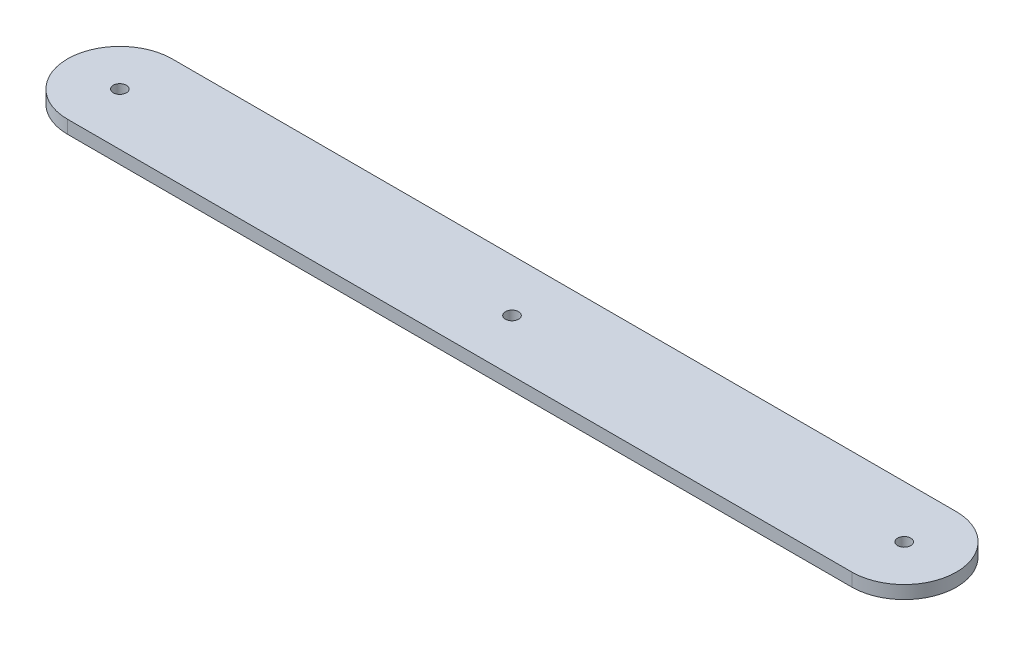
SolidWorks part; units mm, degrees
ref_plane "Front Plane" through (0, 0, 0) normal (0, 0, 1) x (1, 0, 0)
ref_plane "Top Plane" through (0, 0, 0) normal (0, 1, 0) x (1, 0, 0)
ref_plane "Right Plane" through (0, 0, 0) normal (1, 0, 0) x (0, 0, -1)
sketch "Sketch1" plane through (0, 0, 0) normal (0, 1, 0) x (1, 0, 0)
  line L0 (-95.25, 0) -> (95.25, 0) construction
  line L1 (-95.25, 12.7) -> (95.25, 12.7)
  line L2 (-95.25, -12.7) -> (95.25, -12.7)
  arc A0 (-95.25, 12.7) -> (-95.25, -12.7) centre (-95.25, 0) ccw
  arc A1 (95.25, -12.7) -> (95.25, 12.7) centre (95.25, 0) ccw
  circle A2 centre (95.25, 0) radius 2.5797 construction
  circle A3 centre (-95.25, 0) radius 2.5797 construction
  circle A4 centre (0, 0) radius 2.5797 construction
  point P3 (0, 0)
  dimension "D2" = 12.7
  dimension "D3" = 5.1594
  dimension "D1" = 190.5
extrude "Boss-Extrude1" add sketch "Sketch1" along normal blind 3.175
hole_wizard "M3 Clearance Hole1" positions "Sketch2" profile "Sketch3" hole size "M3" standard "ANSI Metric" end condition through all
sketch "Sketch2" plane through (0, 3.175, 0) normal (0, 1, 0) x (1, 0, 0)
  line L0 (95.25, 0) -> (-95.25, 0) construction
  point P0 (-95.25, 0)
  point P2 (0, 0)
  point P5 (95.25, 0)
  dimension "D1" = 190.5
sketch "Sketch3" plane through (-95.25, 3.175, 0) normal (1, 0, 0) x (0, 0, 1)
  line L0 (0, 0) -> (0, 3.175)
  line L1 (0, 3.175) -> (1.6, 3.175)
  line L2 (1.6, 3.175) -> (1.6, 0)
  line L5 (1.6, 0) -> (0, 0)
  line L11 (0, -6.35) -> (0, 107.95) construction
  dimension "Thru Hole Dia." = 3.2
  dimension "Thru Hole Depth" = 3.175
